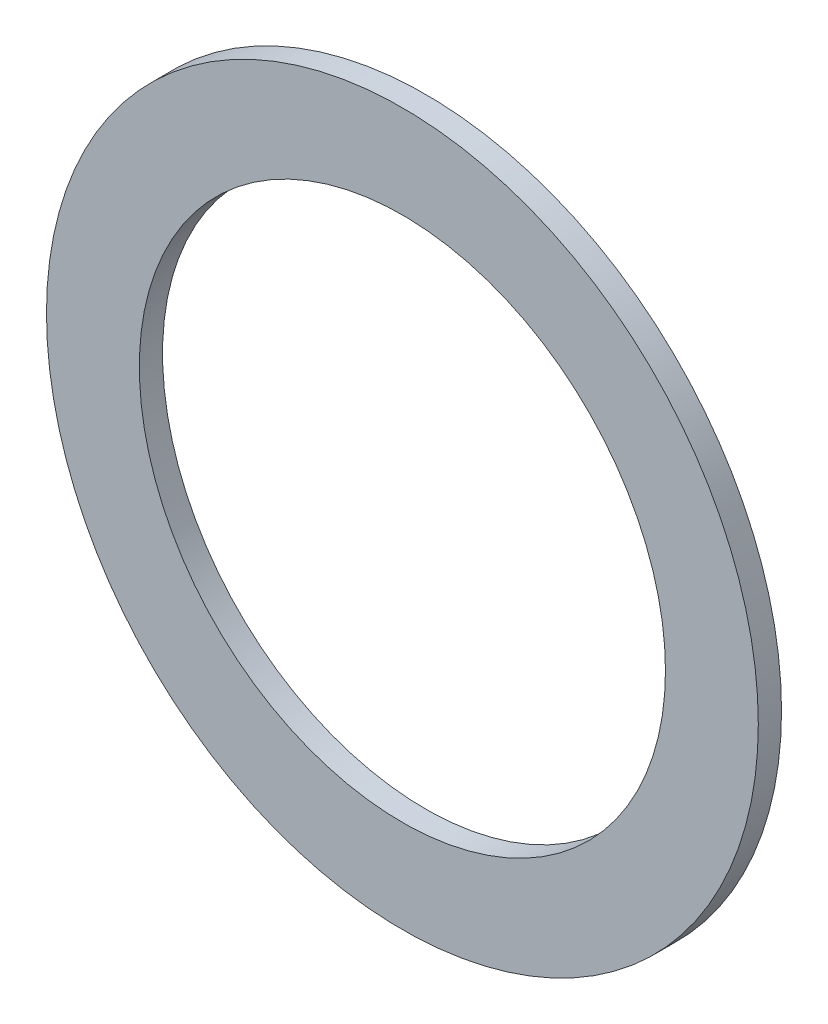
SolidWorks part; units mm, degrees
material "Резина"
ref_plane "Спереди" through (0, 0, 0) normal (0, 0, 1) x (1, 0, 0)
ref_plane "Сверху" through (0, 0, 0) normal (0, 1, 0) x (1, 0, 0)
ref_plane "Справа" through (0, 0, 0) normal (1, 0, 0) x (0, 0, -1)
sketch "Эскиз1" plane through (0, 0, 0) normal (0, 0, 1) x (1, 0, 0)
  circle A2 centre (0, 0) radius 23
  circle A3 centre (0, 0) radius 17
  dimension "D1" = 34
  dimension "D2" = 46
extrude "Бобышка-Вытянуть1" add sketch "Эскиз1" along normal blind 1.5
